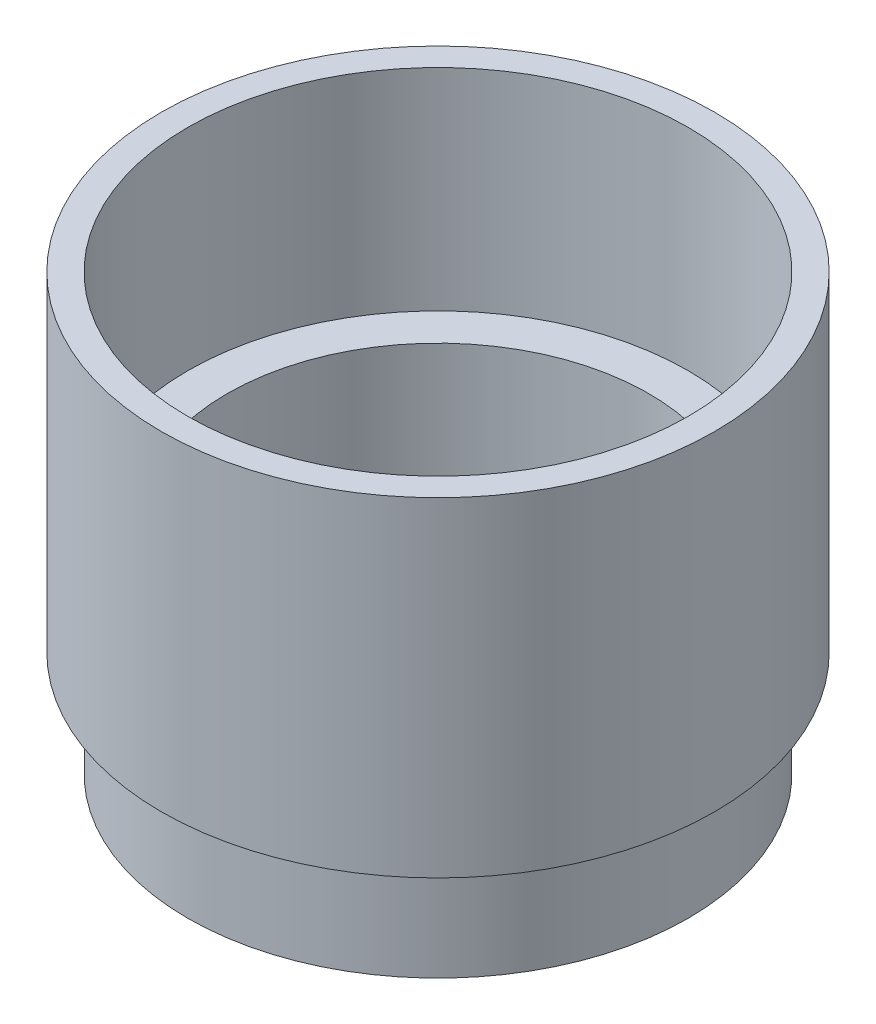
SolidWorks part; units mm, degrees
ref_plane "Front Plane" through (0, 0, 0) normal (0, 0, 1) x (1, 0, 0)
ref_plane "Top Plane" through (0, 0, 0) normal (0, 1, 0) x (1, 0, 0)
ref_plane "Right Plane" through (0, 0, 0) normal (1, 0, 0) x (0, 0, -1)
sketch "Sketch1" plane through (0, 0, 0) normal (0, 0, 1) x (1, 0, 0)
  line L0 (0, -44.45) -> (25.4, -44.45)
  line L1 (25.4, -44.45) -> (25.4, -25.4)
  line L2 (30.1625, 0) -> (33.3375, 0)
  line L3 (33.3375, 0) -> (33.3375, -39.6875)
  line L4 (33.3375, -39.6875) -> (30.1625, -39.6875)
  line L5 (30.1625, -39.6875) -> (30.1625, -52.3875)
  line L6 (30.1625, -52.3875) -> (0, -52.3875)
  line L7 (0, -44.45) -> (0, -52.3875)
  line L8 (25.4, -25.4) -> (30.1625, -25.4)
  line L9 (30.1625, -25.4) -> (30.1625, 0)
  point P3 (0, 0)
  point P12 (1.5653, -14.0599)
  dimension "D1" = 25.4
  dimension "D2" = 33.3375
  dimension "D3" = 30.1625
  dimension "D4" = 12.7
  dimension "D5" = 30.1625
  dimension "D6" = 7.9375
  dimension "D7" = 19.05
  dimension "D8" = 25.4
revolve "Revolve1" add sketch "Sketch1" angle 360 about L7
sketch "Sketch2" plane through (0, -44.45, 0) normal (0, 1, 0) x (1, 0, 0)
  line L1 (12.7, -15.875) -> (-12.7, -15.875)
  line L2 (15.875, -12.7) -> (15.875, 12.7)
  line L3 (12.7, 15.875) -> (-12.7, 15.875)
  line L4 (-15.875, -12.7) -> (-15.875, 12.7)
  line L5 (15.875, -15.875) -> (-15.875, 15.875) construction
  line L6 (15.875, 15.875) -> (-15.875, -15.875) construction
  arc A0 (15.875, 12.7) -> (12.7, 15.875) centre (12.7, 12.7) ccw
  arc A1 (-12.7, 15.875) -> (-15.875, 12.7) centre (-12.7, 12.7) ccw
  arc A2 (-15.875, -12.7) -> (-12.7, -15.875) centre (-12.7, -12.7) ccw
  arc A3 (15.875, -12.7) -> (12.7, -15.875) centre (12.7, -12.7) cw
  point P0 (0, 0)
  dimension "D1" = 3.175
  dimension "D2" = 31.75
extrude "Cut-Extrude1" cut sketch "Sketch2" against normal blind 5.08
